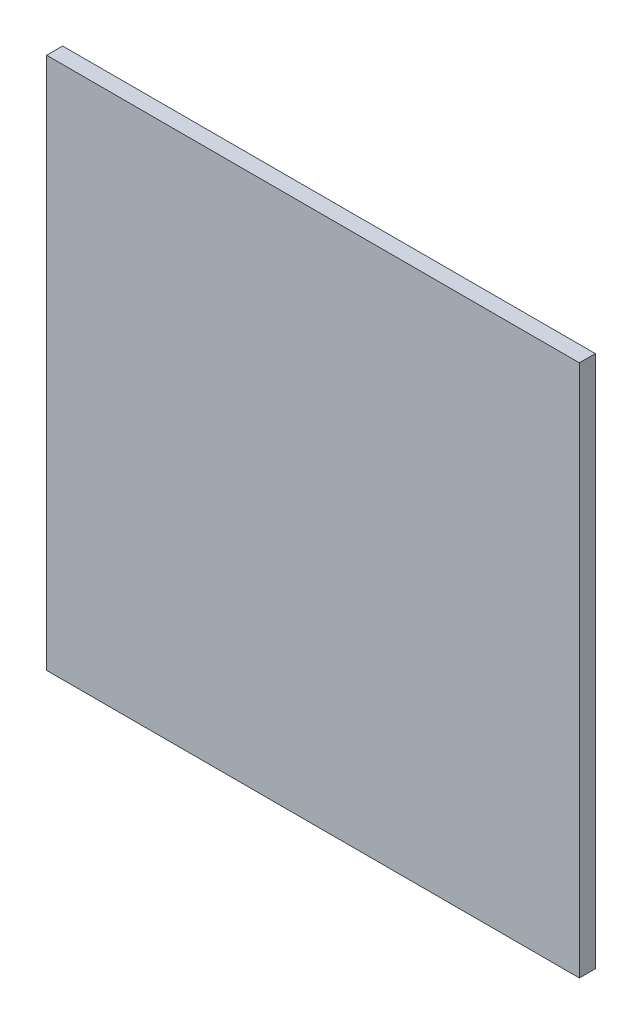
SolidWorks part; units mm, degrees
ref_plane "Front Plane" through (0, 0, 0) normal (0, 0, 1) x (1, 0, 0)
ref_plane "Top Plane" through (0, 0, 0) normal (0, 1, 0) x (1, 0, 0)
ref_plane "Right Plane" through (0, 0, 0) normal (1, 0, 0) x (0, 0, -1)
sketch "Sketch2" plane through (0, 0, 0) normal (0, 0, 1) x (1, 0, 0)
  line L0 (-26.0311, -106.2925) -> (-26.0311, -6.2925)
  line L1 (-26.0311, -6.2925) -> (73.9689, -6.2925)
  line L2 (73.9689, -6.2925) -> (73.9689, -106.2925)
  line L3 (73.9689, -106.2925) -> (-26.0311, -106.2925)
  dimension "D1" = 100
  dimension "D2" = 100
extrude "Boss-Extrude1" add sketch "Sketch2" along normal blind 3
equation "\"R\"= 125mm"
